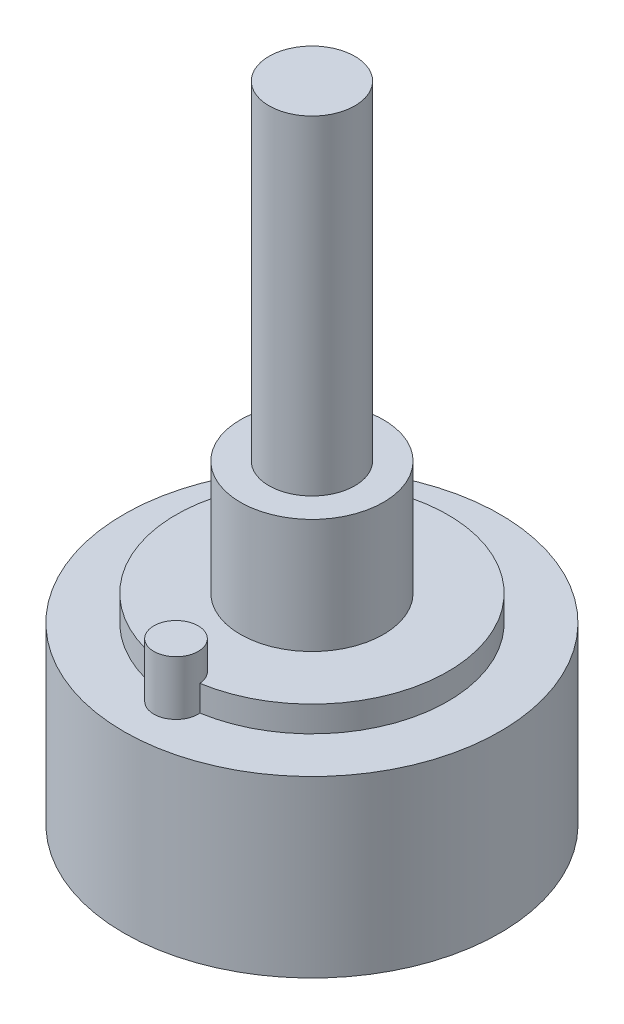
SolidWorks part; units mm, degrees
ref_plane "Front Plane" through (0, 0, 0) normal (0, 0, 1) x (1, 0, 0)
ref_plane "Top Plane" through (0, 0, 0) normal (0, 1, 0) x (1, 0, 0)
ref_plane "Right Plane" through (0, 0, 0) normal (1, 0, 0) x (0, 0, -1)
sketch "Sketch1" plane through (0, 0, 0) normal (0, 1, 0) x (1, 0, 0)
  circle A0 centre (0, 0) radius 13.15
extrude "Boss-Extrude1" add sketch "Sketch1" along normal blind 12.2
sketch "Sketch2" plane through (0, 12.2, 0) normal (0, 1, 0) x (1, 0, 0)
  circle A0 centre (0, 0) radius 9.5
extrude "Boss-Extrude2" add sketch "Sketch2" along normal blind 1.8
sketch "Sketch3" plane through (0, 14, 0) normal (0, 1, 0) x (1, 0, 0)
  circle A0 centre (0, 0) radius 5
extrude "Boss-Extrude3" add sketch "Sketch3" along normal blind 8
sketch "Sketch4" plane through (0, 22, 0) normal (0, 1, 0) x (1, 0, 0)
  circle A0 centre (0, 0) radius 3
extrude "Boss-Extrude4" add sketch "Sketch4" along normal blind 23
sketch "Sketch5" plane through (0, 12.2, 0) normal (0, 1, 0) x (1, 0, 0)
  circle A0 centre (0, -9.5) radius 1.55
  dimension "D1" = 9.5
extrude "Boss-Extrude5" add sketch "Sketch5" along normal blind 3.8
